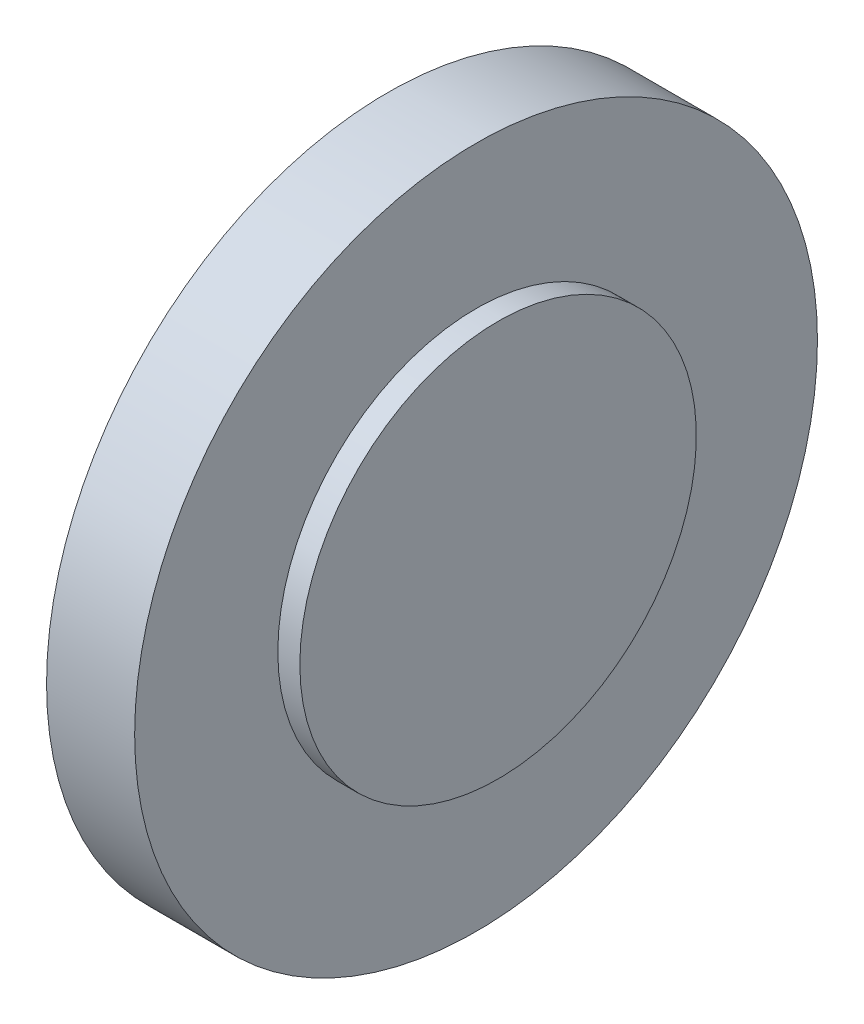
SolidWorks part; units mm, degrees
ref_plane "Front Plane" through (0, 0, 0) normal (0, 0, 1) x (1, 0, 0)
ref_plane "Top Plane" through (0, 0, 0) normal (0, 1, 0) x (1, 0, 0)
ref_plane "Right Plane" through (0, 0, 0) normal (1, 0, 0) x (0, 0, -1)
sketch "Sketch1" plane through (0, 0, 0) normal (0, 0, 1) x (1, 0, 0)
  line L0 (0, 0) -> (97.167, 0) construction
  line L1 (0, 0) -> (0, 46.5)
  line L2 (0, 46.5) -> (12, 46.5)
  line L3 (12, 46.5) -> (12, 27)
  line L4 (12, 27) -> (15, 27)
  line L5 (15, 27) -> (15, 0)
  line L6 (0, 0) -> (15, 0)
  point P3 (0, 0)
  point P9 (0, 0)
  point P10 (0, 0)
  dimension "D1" = 46.5
  dimension "D2" = 27
  dimension "D3" = 3
  dimension "D4" = 12
revolve "Revolve1" add sketch "Sketch1" angle 360 about L0
